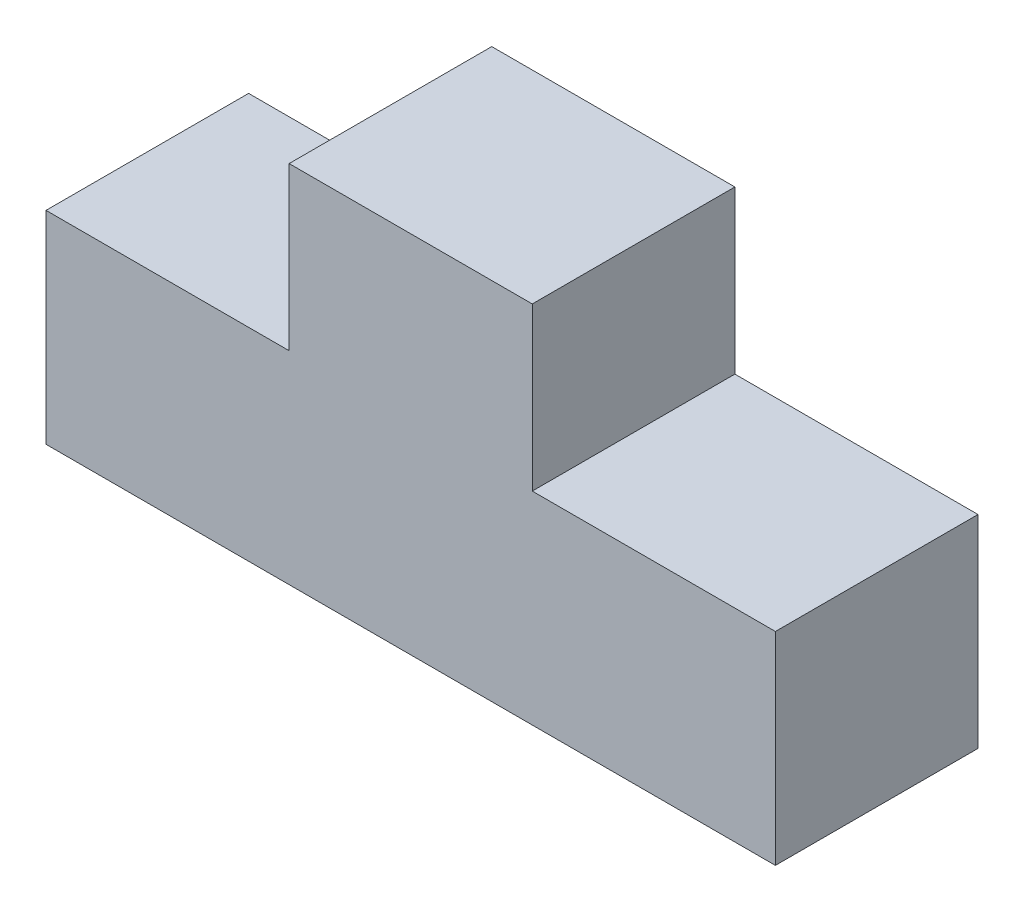
SolidWorks part; units mm, degrees
ref_plane "Front Plane" through (0, 0, 0) normal (0, 0, 1) x (1, 0, 0)
ref_plane "Top Plane" through (0, 0, 0) normal (0, 1, 0) x (1, 0, 0)
ref_plane "Right Plane" through (0, 0, 0) normal (1, 0, 0) x (0, 0, -1)
sketch "Sketch1" plane through (0, 0, 0) normal (0, 0, 1) x (1, 0, 0)
  line L0 (762, 635) -> (762, 1143)
  line L1 (0, 0) -> (2286, 0)
  line L2 (0, 0) -> (0, 635)
  line L3 (0, 635) -> (762, 635)
  line L4 (2286, 0) -> (2286, 635)
  line L5 (762, 1143) -> (1524, 1143)
  line L6 (1524, 1143) -> (1524, 635)
  line L7 (1524, 635) -> (2286, 635)
  dimension "D1" = 635
extrude "Boss-Extrude1" add sketch "Sketch1" against normal blind 635
